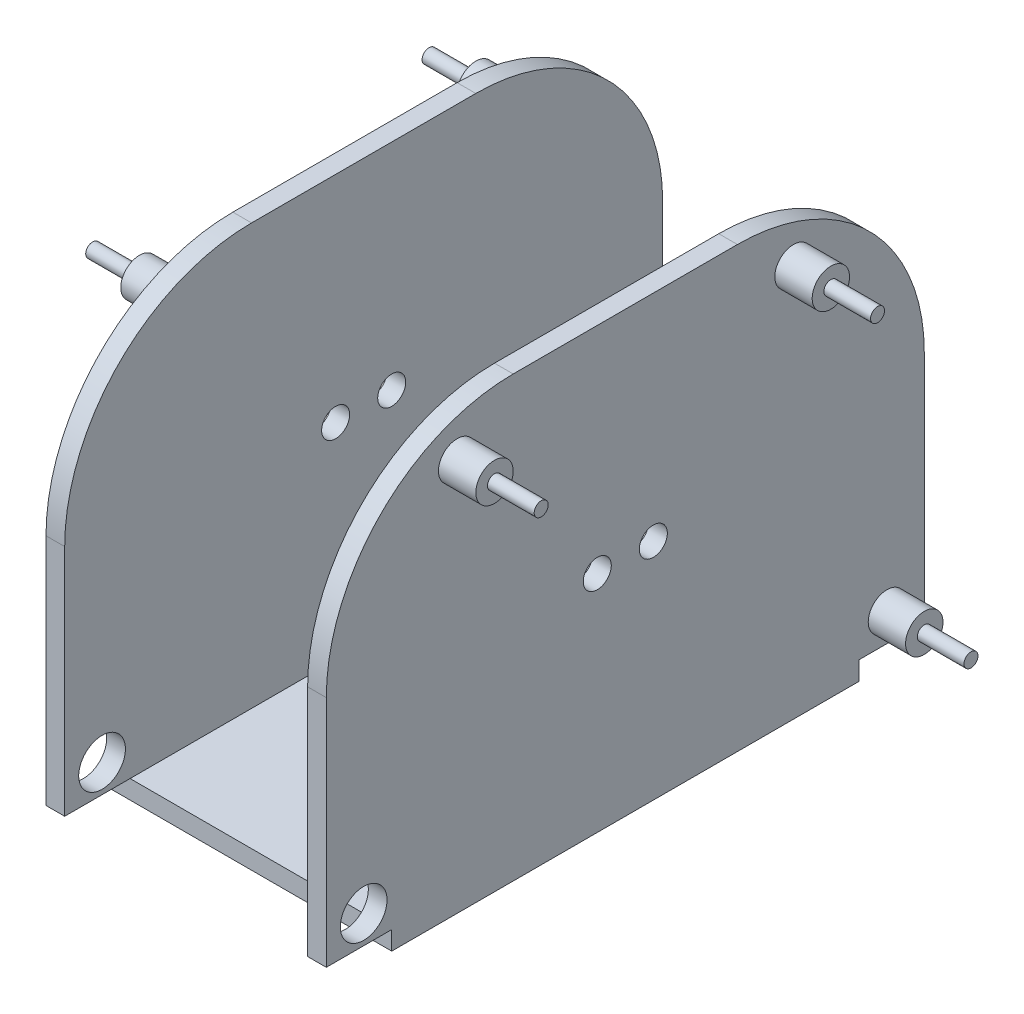
SolidWorks part; units mm, degrees
ref_plane "Front" through (0, 0, 0) normal (0, 0, 1) x (1, 0, 0)
ref_plane "Top" through (0, 0, 0) normal (0, 1, 0) x (1, 0, 0)
ref_plane "Right" through (0, 0, 0) normal (1, 0, 0) x (0, 0, -1)
sketch "草图1" plane through (0, 0, 0) normal (0, 1, 0) x (1, 0, 0)
  line L1 (-15, 25) -> (15, 25)
  line L2 (-15, 25) -> (-15, -25)
  line L3 (-15, -25) -> (15, -25)
  line L4 (15, 25) -> (15, -25)
  dimension "D1" = 30
  dimension "D2" = 50
  dimension "D3" = 15
  dimension "D4" = 25
extrude "凸台-拉伸1" add sketch "草图1" against normal blind 2
sketch "草图3" plane through (0, 0, 0) normal (0, 1, 0) x (1, 0, 0)
  line L1 (-15, 32) -> (-13, 32)
  line L2 (-15, 32) -> (-15, -32)
  line L3 (-15, -32) -> (-13, -32)
  line L4 (-13, 32) -> (-13, -32)
  dimension "D1" = 13
  dimension "D2" = 2
  dimension "D3" = 32
  dimension "D4" = 64
extrude "凸台-拉伸2" add sketch "草图3" along normal blind 45
sketch "草图6" plane through (-13, 0, 0) normal (1, 0, 0) x (0, 0, -1)
  circle A0 centre (-28, 3) radius 2.5
  dimension "D1" = 5
  dimension "D2" = 28
  dimension "D3" = 3
extrude "切除-拉伸1" cut sketch "草图6" against normal through all
sketch "草图7" plane through (-15, 0, 0) normal (-1, 0, 0) x (0, 0, 1)
  line L0 (-32, 45) -> (32, 45) construction
  line L1 (-32, 0) -> (-25, 0) construction
  circle A0 centre (-18, 40) radius 2
  circle A1 centre (18, 40) radius 2
  circle A2 centre (-28, 3) radius 2
  dimension "D1" = 4
  dimension "D2" = 4
  dimension "D3" = 4
  dimension "D4" = 5
  dimension "D5" = 5
  dimension "D6" = 3
  dimension "D7" = 28
  dimension "D8" = 10
  dimension "D9" = 36
extrude "凸台-拉伸4" add sketch "草图7" along normal blind 4
sketch "草图8" plane through (-19, 0, 0) normal (-1, 0, 0) x (0, 0, 1)
  circle A0 centre (-18, 40) radius 0.75
  circle A1 centre (18, 40) radius 0.75
  circle A2 centre (-28, 3) radius 0.75
  dimension "D1" = 1.5
  dimension "D2" = 1.5
  dimension "D3" = 1.5
extrude "凸台-拉伸5" add sketch "草图8" along normal blind 5
fillet "圆角1" radius 20 2 edges at (-14, 45, 32) (-14, 45, -32)
sketch "草图9" plane through (-15, 0, 0) normal (-1, 0, 0) x (0, 0, 1)
  circle A0 centre (-3, 22) radius 1.5
  circle A1 centre (3, 22) radius 1.5
  dimension "D1" = 3
  dimension "D2" = 3
  dimension "D3" = 3
  dimension "D4" = 3
  dimension "D5" = 22
  dimension "D6" = 22
extrude "切除-拉伸2" cut sketch "草图9" against normal through all
ref_plane "基准面2" through (0, 0, 0) normal (-1, 0, 0) x (0, 0, 1)
mirror "镜向1" about plane through (0, 0, 0) normal (-1, 0, 0) of bodies 107
sketch "草图10" plane through (0, 0, 0) normal (0, 1, 0) x (1, 0, 0)
  line L1 (-10, 10) -> (10, 10)
  line L2 (-10, 10) -> (-10, 2)
  line L3 (-10, 2) -> (10, 2)
  line L4 (10, 10) -> (10, 2)
  dimension "D1" = 2
  dimension "D2" = 10
  dimension "D3" = 10
  dimension "D4" = 8
extrude "凸台-拉伸6" add sketch "草图10" along normal blind 5
